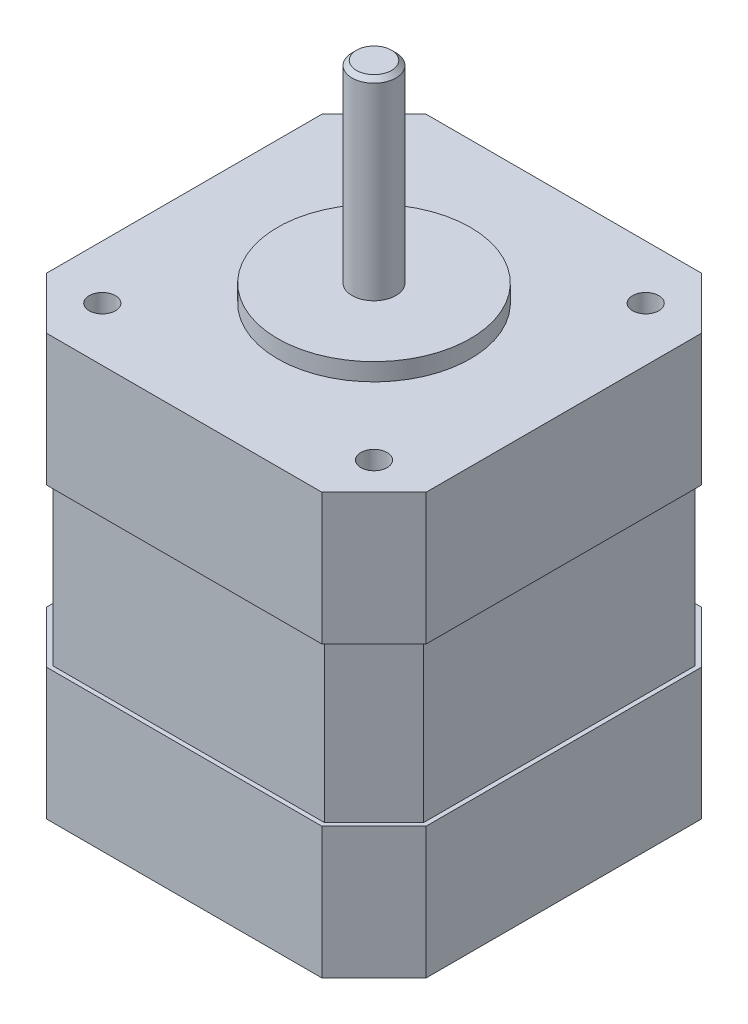
SolidWorks part; units mm, degrees
ref_plane "Front Plane" through (0, 0, 0) normal (0, 0, 1) x (1, 0, 0)
ref_plane "Top Plane" through (0, 0, 0) normal (0, 1, 0) x (1, 0, 0)
ref_plane "Right Plane" through (0, 0, 0) normal (1, 0, 0) x (0, 0, -1)
sketch "Sketch1" plane through (0, 0, 0) normal (0, 1, 0) x (1, 0, 0)
  line L0 (15.5, 21.15) -> (21.15, 15.5)
  line L1 (-15.5, -21.15) -> (15.5, -21.15)
  line L2 (-21.15, -15.5) -> (-21.15, 15.5)
  line L3 (-15.5, 21.15) -> (15.5, 21.15)
  line L4 (21.15, -15.5) -> (21.15, 15.5)
  line L6 (-21.15, -15.5) -> (-15.5, -21.15)
  line L7 (21.15, -15.5) -> (15.5, -21.15)
  line L8 (-15.5, 21.15) -> (-21.15, 15.5)
  point P0 (0, 0)
  dimension "D1" = 42.3
  dimension "D2" = 42.3
  dimension "D3" = 31
  dimension "D4" = 135
  dimension "D6" = 21.15
  dimension "D7" = 21.15
  dimension "D8" = 31
  dimension "D9" = 31
  dimension "D10" = 31
extrude "Boss-Extrude1" add sketch "Sketch1" along normal blind 48 contours L1 L7 L4 L0 L3 L8 L2 L6
sketch "Sketch2" plane through (0, 48, 0) normal (0, 1, 0) x (1, 0, 0)
  circle A0 centre (0, 0) radius 11
  dimension "D1" = 22
extrude "Boss-Extrude2" add sketch "Sketch2" along normal blind 2
sketch "Sketch3" plane through (0, 50, 0) normal (0, 1, 0) x (1, 0, 0)
  circle A0 centre (0, 0) radius 2.5
  dimension "D1" = 5
extrude "Boss-Extrude3" add sketch "Sketch3" along normal blind 22 contours A0
chamfer "Chamfer1" distance 0.5 angle 45 1 edges at (0, 72, 2.5)
sketch "Sketch4" plane through (0, 48, 0) normal (0, 1, 0) x (1, 0, 0)
  line L0 (-21.15, -15.5) -> (-21.15, 15.5) construction
  line L1 (-15.5, 21.15) -> (15.5, 21.15) construction
  circle A0 centre (-15.5, 15.5) radius 1.5
  circle A1 centre (15.5, 15.5) radius 1.5
  circle A2 centre (15.5, -15.5) radius 1.5
  circle A3 centre (-15.5, -15.5) radius 1.5
  point P15 (0, 0)
  dimension "D3" = 3
  dimension "D1" = 5.65
  dimension "D2" = 5.65
  dimension "D4" = 4
extrude "Cut-Extrude1" cut sketch "Sketch4" against normal blind 10
sketch "Sketch6" plane through (0, 48, 0) normal (0, 1, 0) x (1, 0, 0)
  line L16 (-21.65, -15.7071) -> (-15.7071, -21.65)
  line L17 (-15.7071, -21.65) -> (15.7071, -21.65)
  line L18 (15.7071, -21.65) -> (21.65, -15.7071)
  line L19 (21.65, -15.7071) -> (21.65, 15.7071)
  line L20 (21.65, 15.7071) -> (15.7071, 21.65)
  line L21 (15.7071, 21.65) -> (-15.7071, 21.65)
  line L22 (-15.7071, 21.65) -> (-21.65, 15.7071)
  line L23 (-21.65, 15.7071) -> (-21.65, -15.7071)
  line L24 (-21.65, -15.7071) -> (-15.7071, -21.65)
  line L25 (-15.7071, -21.65) -> (15.7071, -21.65)
  line L26 (15.7071, -21.65) -> (21.65, -15.7071)
  line L27 (21.65, -15.7071) -> (21.65, 15.7071)
  line L28 (21.65, 15.7071) -> (15.7071, 21.65)
  line L29 (15.7071, 21.65) -> (-15.7071, 21.65)
  line L30 (-15.7071, 21.65) -> (-21.65, 15.7071)
  line L31 (-21.65, 15.7071) -> (-21.65, -15.7071)
  line L40 (-21.15, -15.5) -> (-15.5, -21.15)
  line L41 (-15.5, -21.15) -> (15.5, -21.15)
  line L42 (15.5, -21.15) -> (21.15, -15.5)
  line L43 (21.15, -15.5) -> (21.15, 15.5)
  line L44 (21.15, 15.5) -> (15.5, 21.15)
  line L45 (15.5, 21.15) -> (-15.5, 21.15)
  line L46 (-15.5, 21.15) -> (-21.15, 15.5)
  line L47 (-21.15, 15.5) -> (-21.15, -15.5)
  line L48 (-21.15, -15.5) -> (-15.5, -21.15)
  line L49 (-15.5, -21.15) -> (15.5, -21.15)
  line L50 (15.5, -21.15) -> (21.15, -15.5)
  line L51 (21.15, -15.5) -> (21.15, 15.5)
  line L52 (21.15, 15.5) -> (15.5, 21.15)
  line L53 (15.5, 21.15) -> (-15.5, 21.15)
  line L54 (-15.5, 21.15) -> (-21.15, 15.5)
  line L55 (-21.15, 15.5) -> (-21.15, -15.5)
  dimension "D1" = 0.5
  dimension "D2" = 0
extrude "Boss-Extrude5" add sketch "Sketch6" against normal blind 15
ref_plane "Plane1" through (0, 24, 0) normal (0, 1, 0) x (1, 0, 0)
mirror "Mirror1" about plane through (0, 24, 0) normal (0, 1, 0) of "Boss-Extrude5"
